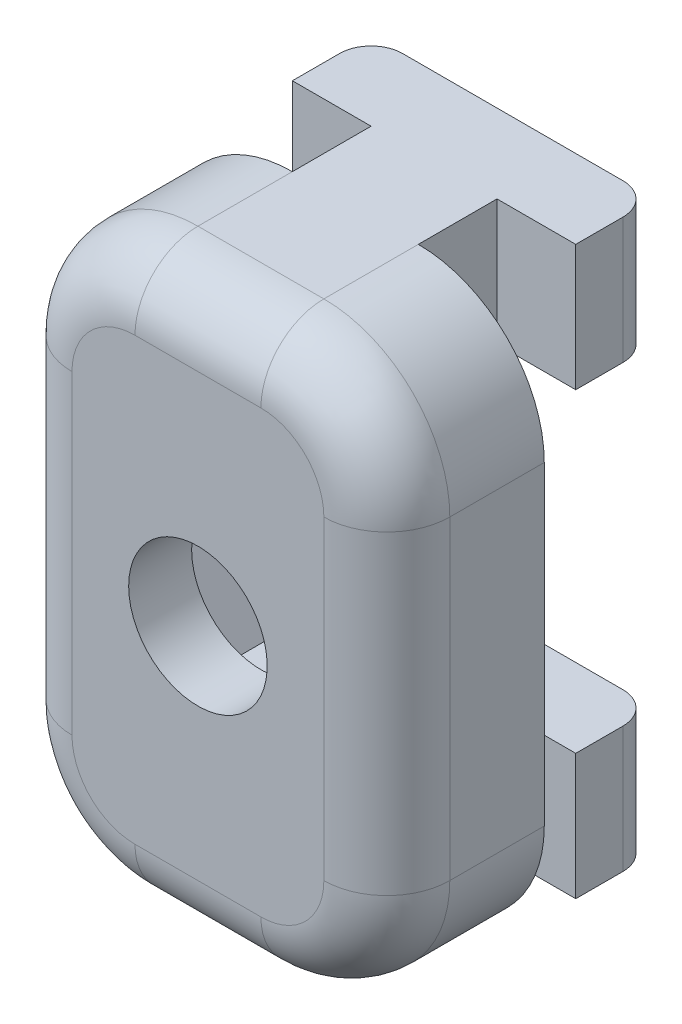
SolidWorks part; units mm, degrees
ref_plane "Plan de face" through (0, 0, 0) normal (0, 0, 1) x (1, 0, 0)
ref_plane "Plan de dessus" through (0, 0, 0) normal (0, 1, 0) x (1, 0, 0)
ref_plane "Plan de droite" through (0, 0, 0) normal (1, 0, 0) x (0, 0, -1)
sketch "Esquisse2" plane through (0, 0, 0) normal (0, 1, 0) x (1, 0, 0)
  line L1 (11.5687, 38.1282) -> (18.5687, 38.1282)
  line L2 (10.5687, 37.1282) -> (10.5687, 35.6282)
  line L3 (10.5687, 35.6282) -> (13.0687, 35.6282)
  line L4 (19.5687, 37.1282) -> (19.5687, 35.6282)
  line L7 (13.0687, 33.1282) -> (13.0687, 35.6282)
  line L9 (17.0687, 33.1282) -> (17.0687, 35.6282)
  line L10 (17.0687, 35.6282) -> (19.5687, 35.6282)
  line L11 (17.0687, 33.1282) -> (21.0687, 33.1282)
  line L12 (9.0687, 33.1282) -> (13.0687, 33.1282)
  line L13 (9.0687, 33.1282) -> (9.0687, 28.1282)
  line L14 (9.0687, 28.1282) -> (21.0687, 28.1282)
  line L15 (21.0687, 33.1282) -> (21.0687, 28.1282)
  arc A0 (18.5687, 38.1282) -> (19.5687, 37.1282) centre (18.5687, 37.1282) cw
  arc A1 (11.5687, 38.1282) -> (10.5687, 37.1282) centre (11.5687, 37.1282) ccw
  point P12 (15.0687, 38.1282)
  point P13 (15.0687, 28.1282)
  point P16 (19.5687, 38.1282)
  point P19 (10.5687, 38.1282)
  dimension "D4" = 1
  dimension "D1" = 9
  dimension "D2" = 2.5
  dimension "D3" = 4
  dimension "D5" = 2.5
  dimension "D6" = 12
  dimension "D7" = 5
extrude "Boss.-Extru.3" add sketch "Esquisse2" along normal blind 4
sketch "Esquisse3" plane through (0, 4, 0) normal (0, 1, 0) x (1, 0, 0)
  line L1 (9.0687, 33.1282) -> (21.0687, 33.1282)
  line L2 (9.0687, 33.1282) -> (9.0687, 28.1282)
  line L3 (9.0687, 28.1282) -> (21.0687, 28.1282)
  line L4 (21.0687, 33.1282) -> (21.0687, 28.1282)
extrude "Boss.-Extru.4" add sketch "Esquisse3" along normal blind 5
mirror "Symétrie1" about plane through (0, 9, 0) normal (0, 1, 0) of bodies 104
sketch "Esquisse4" plane through (0, 0, -33.1282) normal (0, 0, -1) x (-1, 0, 0)
  line L0 (-15.0687, 18) -> (-15.0687, 0) construction
  line L1 (-18.5687, 18) -> (-11.5687, 18) construction
  line L2 (-18.5687, 0) -> (-11.5687, 0) construction
  circle A0 centre (-15.0687, 9) radius 2.2
  dimension "D1" = 4.4
extrude "Enlèv. mat.-Extru.1" cut sketch "Esquisse4" against normal up to next
sketch "Esquisse5" plane through (0, 0, -33.1282) normal (0, 0, -1) x (-1, 0, 0)
  line L6 (-13.048, 12.5) -> (-17.0895, 12.5)
  line L7 (-17.0895, 12.5) -> (-19.1102, 9)
  line L8 (-19.1102, 9) -> (-17.0895, 5.5)
  line L9 (-17.0895, 5.5) -> (-13.048, 5.5)
  line L10 (-13.048, 5.5) -> (-11.0273, 9)
  line L11 (-11.0273, 9) -> (-13.048, 12.5)
  line L12 (-19.1102, 9) -> (-11.0273, 9) construction
  point P3 (-15.0687, 5.5)
  point P7 (-15.0687, 9)
  point P10 (-15.0687, 9)
  dimension "D1" = 7
  dimension "D2" = 120
  dimension "D3" = 7
extrude "Enlèv. mat.-Extru.2" cut sketch "Esquisse5" against normal blind 3
fillet "Congé1" radius 4 4 edges at (9.0687, 0, -30.6282) (9.0687, 18, -30.6282) (21.0687, 18, -30.6282) (21.0687, 0, -30.6282)
fillet "Congé2" radius 2 8 edges at (21.0687, 9, -28.1282) (19.8972, 1.1716, -28.1282) (15.0687, 0, -28.1282) (10.2403, 1.1716, -28.1282) (9.0687, 9, -28.1282) (10.2403, 16.8284, -28.1282) (15.0687, 18, -28.1282) (19.8972, 16.8284, -28.1282)
